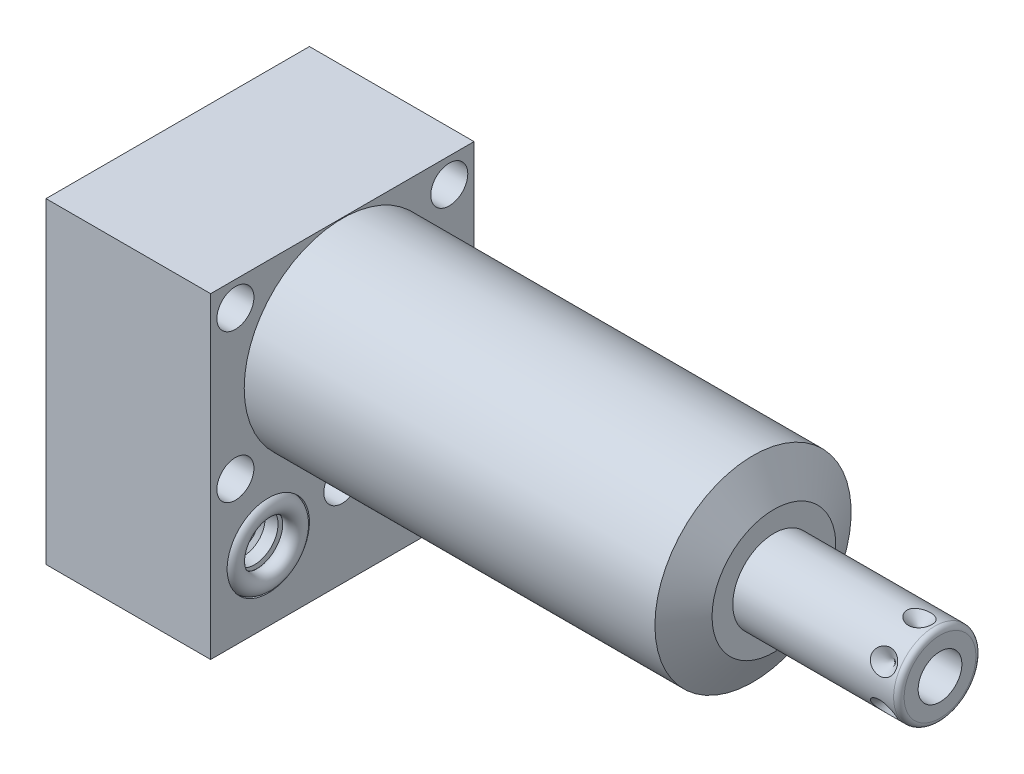
SolidWorks part; units mm, degrees
material "Alloy Steel"
ref_plane "Front Plane" through (0, 0, 0) normal (0, 0, 1) x (1, 0, 0)
ref_plane "Top Plane" through (0, 0, 0) normal (0, 1, 0) x (1, 0, 0)
ref_plane "Right Plane" through (0, 0, 0) normal (1, 0, 0) x (0, 0, -1)
ref_plane "Plane1" through (0, 0, 0) normal (1, 0, 0) x (0, 0, -1)
sketch "Sketch1" plane through (0, 0, 0) normal (1, 0, 0) x (0, 0, -1)
  line L0 (-25.4, 19.05) -> (-25.4, -42.0624)
  line L1 (-25.4, -42.0624) -> (25.4, -42.0624)
  line L2 (25.4, -42.0624) -> (25.4, 19.05)
  line L3 (25.4, 19.05) -> (-25.4, 19.05)
  line L4 (0, -47.0916) -> (0, 22.1996) construction
  dimension "D1" = 50.8
  dimension "D2" = 61.1124
  dimension "D3" = 19.05
extrude "Extrude1" add sketch "Sketch1" along normal blind 83.2358 and the other way blind 31.75
ref_plane "Plane2" through (0, 0, 0) normal (1, 0, 0) x (0, 0, -1)
sketch "Sketch2" plane through (0, 0, 0) normal (1, 0, 0) x (0, 0, -1)
  line L0 (-20.8153, 0) -> (20.8153, 0) construction
  line L6 (25.4, 19.05) -> (-25.4, 19.05)
  line L7 (-25.4, 19.05) -> (-25.4, -42.0624)
  line L8 (-25.4, -42.0624) -> (25.4, -42.0624)
  line L9 (25.4, -42.0624) -> (25.4, 19.05)
  line L10 (25.4, 19.05) -> (-25.4, 19.05)
  line L11 (-25.4, 19.05) -> (-25.4, -42.0624)
  line L12 (-25.4, -42.0624) -> (25.4, -42.0624)
  line L13 (25.4, -42.0624) -> (25.4, 19.05)
  circle A0 centre (0, 0) radius 18.923
  dimension "D1" = 37.846
  dimension "D2" = 0
extrude "Cut-Extrude1" cut sketch "Sketch2" along normal up to next
ref_plane "Plane3" through (0, 0, 0) normal (0, 0, 1) x (1, 0, 0)
sketch "Sketch3" plane through (0, 0, 0) normal (0, 0, 1) x (1, 0, 0)
  line L0 (79.203, 18.923) -> (83.2358, 11.938)
  line L1 (56.7002, 0) -> (61.1362, 0) construction
  line L2 (83.2358, 18.923) -> (83.2358, 11.938)
  line L3 (83.2358, 18.923) -> (79.203, 18.923)
  line L4 (83.2358, 18.923) -> (0, 18.923) construction
  line L5 (83.2358, -18.923) -> (83.2358, 18.923) construction
  dimension "D1" = 23.876
  dimension "D2" = 30
revolve "Cut-Revolve1" cut sketch "Sketch3" angle 360 about L1
ref_plane "Plane4" through (-29.083, -28.575, 14.2748) normal (0, 0, 1) x (0, 1, 0)
sketch "S2D0002" plane through (-29.083, -28.575, 14.2748) normal (0, 0, 1) x (0, 1, 0)
  line L0 (0, 0) -> (4.5466, 0)
  line L1 (4.5466, 0) -> (4.1066, -2.0701)
  line L2 (4.1066, -2.0701) -> (3.4544, -2.7223)
  line L3 (3.4544, -2.7223) -> (3.4544, -13.97)
  line L4 (3.4544, -13.97) -> (0, -13.97)
  line L5 (0, -13.97) -> (0, 0)
  line L6 (0, -14.6685) -> (0, 0.6985) construction
  dimension "D1" = 13.97
revolve "Cut-Revolve2" cut sketch "S2D0002" angle 360 about L6
ref_plane "Plane5" through (-29.083, -28.575, -14.2748) normal (0, 0, 1) x (0, 1, 0)
sketch "Sketch5" plane through (-29.083, -28.575, -14.2748) normal (0, 0, 1) x (0, 1, 0)
  line L0 (0, 0) -> (4.5466, 0)
  line L1 (4.5466, 0) -> (4.1066, -2.0701)
  line L2 (4.1066, -2.0701) -> (3.4544, -2.7223)
  line L3 (3.4544, -2.7223) -> (3.4544, -13.97)
  line L4 (3.4544, -13.97) -> (0, -13.97)
  line L5 (0, -13.97) -> (0, 0)
  line L6 (0, -14.6685) -> (0, 0.6985) construction
  dimension "D1" = 13.97
revolve "Cut-Revolve3" cut sketch "Sketch5" angle 360 about L6
ref_plane "Plane6" through (-2.667, -28.575, 14.2748) normal (0, 0, 1) x (0, -1, 0)
sketch "Sketch6" plane through (-2.667, -28.575, 14.2748) normal (0, 0, 1) x (0, -1, 0)
  line L0 (0, 0) -> (4.5466, 0)
  line L1 (4.5466, 0) -> (4.1066, -2.0701)
  line L2 (4.1066, -2.0701) -> (3.4544, -2.7223)
  line L3 (3.4544, -2.7223) -> (3.4544, -12.192)
  line L4 (3.4544, -12.192) -> (0, -12.192)
  line L5 (0, -12.192) -> (0, 0)
  line L6 (0, -12.8016) -> (0, 0.6096) construction
  dimension "D1" = 12.192
revolve "Cut-Revolve4" cut sketch "Sketch6" angle 360 about L6
ref_plane "Plane7" through (-2.667, -28.575, -14.2748) normal (0, 0, 1) x (0, -1, 0)
sketch "Sketch7" plane through (-2.667, -28.575, -14.2748) normal (0, 0, 1) x (0, -1, 0)
  line L0 (0, 0) -> (4.5466, 0)
  line L1 (4.5466, 0) -> (4.1066, -2.0701)
  line L2 (4.1066, -2.0701) -> (3.4544, -2.7223)
  line L3 (3.4544, -2.7223) -> (3.4544, -12.192)
  line L4 (3.4544, -12.192) -> (0, -12.192)
  line L5 (0, -12.192) -> (0, 0)
  line L6 (0, -12.8016) -> (0, 0.6096) construction
  dimension "D1" = 12.192
revolve "Cut-Revolve5" cut sketch "Sketch7" angle 360 about L6
ref_plane "Plane8" through (-15.875, -43.688, 14.2748) normal (0, 0, 1) x (-1, 0, 0)
sketch "Sketch18" plane through (-31.75, 0, 0) normal (-1, 0, 0) x (0, 0, 1)
  circle A0 centre (-14.2748, -28.575) radius 7.9375
  circle A1 centre (14.2748, -28.575) radius 7.9375
  dimension "D1" = 15.875
  dimension "D2" = 15.875
extrude "Cut-Extrude2" cut sketch "Sketch18" against normal blind 2.667
sketch "Sketch19" plane through (0, 0, 0) normal (1, 0, 0) x (0, 0, -1)
  circle A0 centre (-14.2748, -28.575) radius 7.9375
  circle A1 centre (14.2748, -28.575) radius 7.9375
  dimension "D1" = 15.875
  dimension "D2" = 15.875
extrude "Cut-Extrude3" cut sketch "Sketch19" against normal blind 2.667
sketch "Sketch8" plane through (-15.875, -43.688, 14.2748) normal (0, 0, 1) x (-1, 0, 0)
  line L0 (0, -1.8796) -> (6.1849, -1.8796)
  line L1 (6.1849, -1.8796) -> (5.6423, -4.4323)
  line L2 (5.6423, -4.4323) -> (4.9784, -5.0962)
  line L3 (4.9784, -5.0962) -> (4.9784, -20.9296)
  line L4 (4.9784, -20.9296) -> (0, -20.9296)
  line L5 (0, -20.9296) -> (0, -1.8796)
  line L6 (0, -26.67) -> (0, 1.27) construction
  line L7 (15.875, -1.6256) -> (-15.875, -1.6256) construction
  dimension "D1" = 19.05
  dimension "D2" = 0.254
revolve "Cut-Revolve6" cut sketch "Sketch8" angle 360 about L6
ref_plane "Plane9" through (-15.875, -43.688, -14.2748) normal (0, 0, 1) x (-1, 0, 0)
sketch "Sketch9" plane through (-15.875, -43.688, -14.2748) normal (0, 0, 1) x (-1, 0, 0)
  line L0 (0, -1.8796) -> (6.1849, -1.8796)
  line L1 (6.1849, -1.8796) -> (5.6423, -4.4323)
  line L2 (5.6423, -4.4323) -> (4.9784, -5.0962)
  line L3 (4.9784, -5.0962) -> (4.9784, -20.9296)
  line L4 (4.9784, -20.9296) -> (0, -20.9296)
  line L5 (0, -20.9296) -> (0, -1.8796)
  line L6 (0, -26.67) -> (0, 1.27) construction
  line L7 (15.875, -1.6256) -> (-15.875, -1.6256) construction
  dimension "D1" = 19.05
  dimension "D2" = 0.254
revolve "Cut-Revolve7" cut sketch "Sketch9" angle 360 about L6
ref_plane "Plane10" through (0, 0, 0) normal (0, 0, 1) x (1, 0, 0)
sketch "Sketch20" plane through (0, -42.0624, 0) normal (0, -1, 0) x (1, 0, 0)
  circle A0 centre (-15.875, 14.2748) radius 9.525
  circle A1 centre (-15.875, -14.2748) radius 9.525
  dimension "D1" = 19.05
extrude "Cut-Extrude4" cut sketch "Sketch20" against normal blind 0.254
sketch "Sketch10" plane through (0, 0, 0) normal (0, 0, 1) x (1, 0, 0)
  line L0 (83.2358, 0) -> (83.2358, 7.9375)
  line L1 (83.2358, 7.9375) -> (114.2492, 7.9375)
  line L2 (115.2652, 6.9215) -> (115.2652, 0)
  line L3 (115.2652, 0) -> (83.2358, 0)
  line L4 (59.5935, 0) -> (89.0981, 0) construction
  line L5 (83.2358, -11.938) -> (83.2358, 11.938) construction
  line L6 (-31.75, 19.05) -> (-31.75, -42.0624) construction
  arc A0 (115.2652, 6.9215) -> (114.2492, 7.9375) centre (114.2492, 6.9215) ccw
  point P0 (60.9346, 0)
  dimension "D2" = 1.016
  dimension "D1" = 15.875
  dimension "D3" = 147.0152
revolve "Revolve1" add sketch "Sketch10" angle 360 about L4
ref_plane "Plane11" through (87.757, -4.2164, 0) normal (0, 0, 1) x (0, -1, 0)
sketch "S2D0001" plane through (87.757, -4.2164, 0) normal (0, 0, 1) x (0, -1, 0)
  line L0 (0, 27.5082) -> (0, 12.2682)
  line L1 (0, 12.2682) -> (-4.2164, 9.7347)
  line L2 (0, 27.5082) -> (-4.2164, 27.5082)
  line L3 (-4.2164, 27.5082) -> (-4.2164, 9.7347)
  line L4 (-4.2164, -24.865) -> (-4.2164, 0.8887) construction
  line L5 (2.7051, 27.5082) -> (-11.1379, 27.5082) construction
  dimension "D1" = 8.4328
  dimension "D2" = 59
  dimension "D3" = 15.24
revolve "Cut-Revolve8" cut sketch "S2D0001" angle 360 about L4
ref_plane "Plane14" through (0, -28.575, -14.2748) normal (0, -1, 0) x (0, 0, -1)
sketch "Sketch14" plane through (0, -28.575, -14.2748) normal (0, -1, 0) x (0, 0, -1)
  line L0 (0, -2.8435) -> (0, 1.0401) construction
  line L1 (0, -2.667) -> (0, -4.7371) construction
  line L2 (7.9375, -2.667) -> (-7.9375, -2.667) construction
  circle A0 centre (6.1722, -0.9017) radius 1.7653
  dimension "D1" = 3.5306
  dimension "D2" = 12.3444
revolve "Revolve2" add sketch "Sketch14" angle 360 about L0
ref_plane "Plane15" through (0, -28.575, -14.2748) normal (0, -1, 0) x (0, 0, -1)
sketch "Sketch15" plane through (0, -28.575, -14.2748) normal (0, -1, 0) x (0, 0, -1)
  line L0 (0, -32.7901) -> (0, -28.9065) construction
  line L1 (0, -26.3607) -> (0, -19.4599) construction
  line L2 (-7.9375, -29.083) -> (7.9375, -29.083) construction
  circle A0 centre (6.1722, -30.8483) radius 1.7653
  dimension "D1" = 3.5306
  dimension "D2" = 12.3444
revolve "Revolve3" add sketch "Sketch15" angle 360 about L0
ref_plane "Plane16" through (83.7946, -7.9375, 0) normal (0, 0, 1) x (-1, 0, 0)
sketch "Sketch16" plane through (83.7946, -7.9375, 0) normal (0, 0, 1) x (-1, 0, 0)
  line L0 (-27.5082, 0) -> (-25.0952, 0)
  line L1 (-25.0952, 0) -> (-27.5082, -2.413)
  line L2 (-27.5082, 0) -> (-27.5082, -2.413)
  line L3 (-27.5082, -3.8054) -> (-27.5082, 0.1207) construction
  line L4 (0.5588, 0) -> (-30.4546, 0) construction
  line L5 (-31.4706, -1.016) -> (-31.4706, -14.859) construction
  dimension "D1" = 3.9624
  dimension "D2" = 4.826
  dimension "D3" = 45
revolve "Cut-Revolve9" cut sketch "Sketch16" angle 360 about L3
pattern_circular "CirPattern1" count 6 over 360 about axis through (83.2368, 0, 0) along (-1, 0, 0) of "Cut-Revolve9"
hole_wizard "Hole1" positions "Sketch22" profile "Sketch21" legacy end condition up to next
sketch "Sketch22" plane through (0, 0, 0) normal (1, 0, 0) x (0, 0, -1)
  line L0 (0, 0) -> (-32.1908, 0) construction
  point P0 (-20.6248, 14.2748)
  point P1 (0, -25.0952)
  point P13 (-20.6248, -14.2748)
  point P14 (20.6248, 14.2748)
  point P15 (20.6248, -14.2748)
  dimension "D2" = 14.2748
  dimension "D3" = 25.0952
sketch "Sketch21" plane through (0, 14.2748, 20.6248) normal (0, 1, 0) x (0, 0, -1)
  line L0 (0, 0) -> (0, 31.75)
  line L1 (0, 31.75) -> (3.5687, 31.75)
  line L2 (3.5687, 31.75) -> (3.5687, 0)
  line L3 (3.5687, 0) -> (0, 0)
  line L4 (0, 110) -> (0, -10) construction
  dimension "Diameter" = 7.1374
  dimension "Depth" = 31.75
pattern_linear "LPattern1" count 2 spacing 28.5496 along (0, 0, 1) of "Revolve3", "Revolve2"
